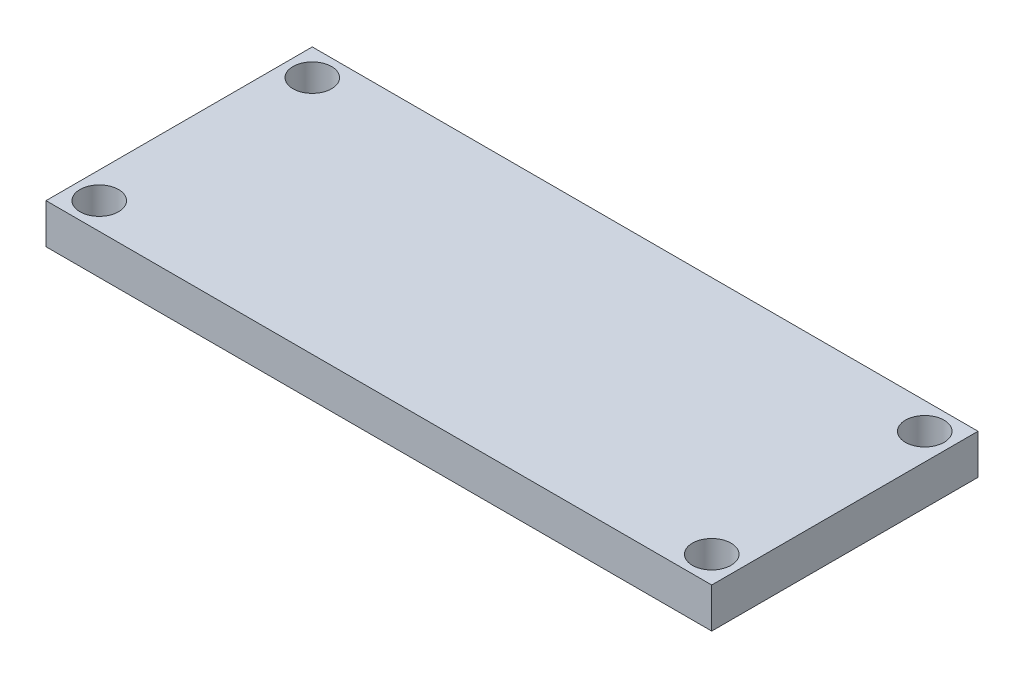
SolidWorks part; units mm, degrees
ref_plane "Front Plane" through (0, 0, 0) normal (0, 0, 1) x (1, 0, 0)
ref_plane "Top Plane" through (0, 0, 0) normal (0, 1, 0) x (1, 0, 0)
ref_plane "Right Plane" through (0, 0, 0) normal (1, 0, 0) x (0, 0, -1)
sketch "Sketch1" plane through (0, 0, 0) normal (0, 1, 0) x (1, 0, 0)
  line L1 (-20.9859, 11.4085) -> (29.0141, 11.4085)
  line L2 (-20.9859, 11.4085) -> (-20.9859, -8.5915)
  line L3 (-20.9859, -8.5915) -> (29.0141, -8.5915)
  line L4 (29.0141, 11.4085) -> (29.0141, -8.5915)
  dimension "D1" = 20
  dimension "D2" = 50
extrude "Boss-Extrude1" add sketch "Sketch1" along normal blind 3
sketch "Sketch2" plane through (0, 3, 0) normal (0, 1, 0) x (1, 0, 0)
  line L0 (29.0141, 11.4085) -> (-20.9859, 11.4085) construction
  line L1 (29.0141, -8.5915) -> (29.0141, 11.4085) construction
  line L2 (-20.9859, -8.5915) -> (29.0141, -8.5915) construction
  line L3 (-20.9859, 11.4085) -> (-20.9859, -8.5915) construction
  circle A0 centre (-18.9859, -6.5915) radius 1.25
  circle A1 centre (-18.9859, 9.4085) radius 1.25
  circle A2 centre (27.0141, -6.5915) radius 1.25
  circle A3 centre (27.0141, 9.4085) radius 1.25
  dimension "D1" = 2.5
  dimension "D2" = 2.5
  dimension "D3" = 2.5
  dimension "D4" = 2.5
  dimension "D5" = 2
  dimension "D6" = 2
  dimension "D7" = 2
  dimension "D8" = 2
  dimension "D9" = 2
  dimension "D10" = 2
  dimension "D11" = 2
  dimension "D12" = 2
  dimension "D13" = 2
hole_wizard "M2.5 Clearance Hole1" positions "Sketch3" profile "Sketch4" hole size "M2.5" standard "ANSI Metric"
sketch "Sketch3" plane through (0, 3, 0) normal (0, 1, 0) x (1, 0, 0)
  point P0 (-18.9859, -6.5915)
  point P3 (-18.9859, 9.4085)
  point P6 (27.0141, -6.5915)
  point P9 (27.0141, 9.4085)
sketch "Sketch4" plane through (-18.9859, 3, 6.5915) normal (1, 0, 0) x (0, 0, 1)
  line L0 (0, 0) -> (0, 3.8712)
  line L1 (0, 3.8712) -> (1.45, 3)
  line L2 (1.45, 3) -> (1.45, 0)
  line L5 (1.45, 0) -> (0, 0)
  line L10 (0, 3.8712) -> (-1.45, 3) construction
  line L11 (0, -6.35) -> (0, 107.95) construction
  dimension "Hole Dia." = 2.9
  dimension "Hole Depth" = 3
  dimension "Drill Angle" = 118
